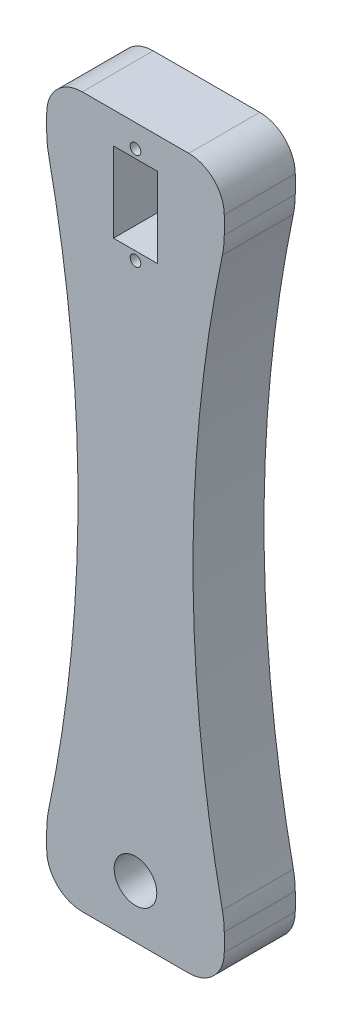
SolidWorks part; units mm, degrees
ref_plane "Front Plane" through (0, 0, 0) normal (0, 0, 1) x (1, 0, 0)
ref_plane "Top Plane" through (0, 0, 0) normal (0, 1, 0) x (1, 0, 0)
ref_plane "Right Plane" through (0, 0, 0) normal (1, 0, 0) x (0, 0, -1)
sketch "Sketch1" plane through (0, 0, 0) normal (0, 0, 1) x (1, 0, 0)
  line L1 (0, 0) -> (50, 0)
  line L2 (0, 0) -> (0, -200)
  line L3 (0, -200) -> (50, -200)
  line L4 (50, 0) -> (50, -200)
extrude "Boss-Extrude1" add sketch "Sketch1" along normal blind 20
sketch "Sketch2" plane through (0, 0, 20) normal (0, 0, 1) x (1, 0, 0)
  circle A0 centre (25, -185) radius 6
  circle A1 centre (25, -15) radius 6
extrude "Cut-Extrude1" cut sketch "Sketch2" against normal blind 84
fillet "Fillet1" radius 10 4 edges at (0, -200, 10) (0, 0, 10) (50, 0, 10) (50, -200, 10)
sketch "Sketch4" plane through (0, 0, 20) normal (0, 0, 1) x (1, 0, 0)
  line L1 (25, -8.8) -> (31.2, -8.8)
  line L3 (25, -31.3) -> (18.8, -31.3)
  line L4 (31.2, -8.8) -> (31.2, -31.3)
  line L5 (31.2, -31.3) -> (18.8, -31.3)
  line L6 (18.8, -31.3) -> (18.8, -8.8)
  line L7 (18.8, -8.8) -> (25, -8.8)
  circle A0 centre (25, -6.4) radius 1.5
  circle A1 centre (25, -33.7) radius 1.5
  circle M13 centre (25, -15) radius 6
extrude "Cut-Extrude2" cut sketch "Sketch4" against normal blind 33 contours L7 L6 L3 L5 L4 L1 M13 | A1 | A0
sketch "Sketch5" plane through (0, 0, 20) normal (0, 0, 1) x (1, 0, 0)
  line L2 (50, -185) -> (50, -10)
  line L3 (50, -190) -> (50, -10) construction
  line L4 (0, -10) -> (0, -190)
  arc A0 (0, -15) -> (0.53, -20.1205) centre (25, -15) ccw
  arc A1 (50, -185) -> (49.47, -179.8795) centre (25, -185) ccw
  arc A2 (49.47, -20.1205) -> (49.47, -179.8795) centre (431.2019, -100) ccw
  arc A3 (0.53, -179.8795) -> (0.53, -20.1205) centre (-381.2019, -100) ccw
  arc A4 (50, -10) -> (40, 0) centre (40, -10) ccw construction
  arc A5 (0.53, -179.8795) -> (0, -185) centre (25, -185) ccw
  arc A6 (49.47, -20.1205) -> (50, -15) centre (25, -15) ccw
  line M12 (50, -190) -> (50, -10)
extrude "Cut-Extrude3" cut sketch "Sketch5" against normal blind 53 and the other way through all contours A6 A2 A1 M12 | A5 A3 A0 L4
